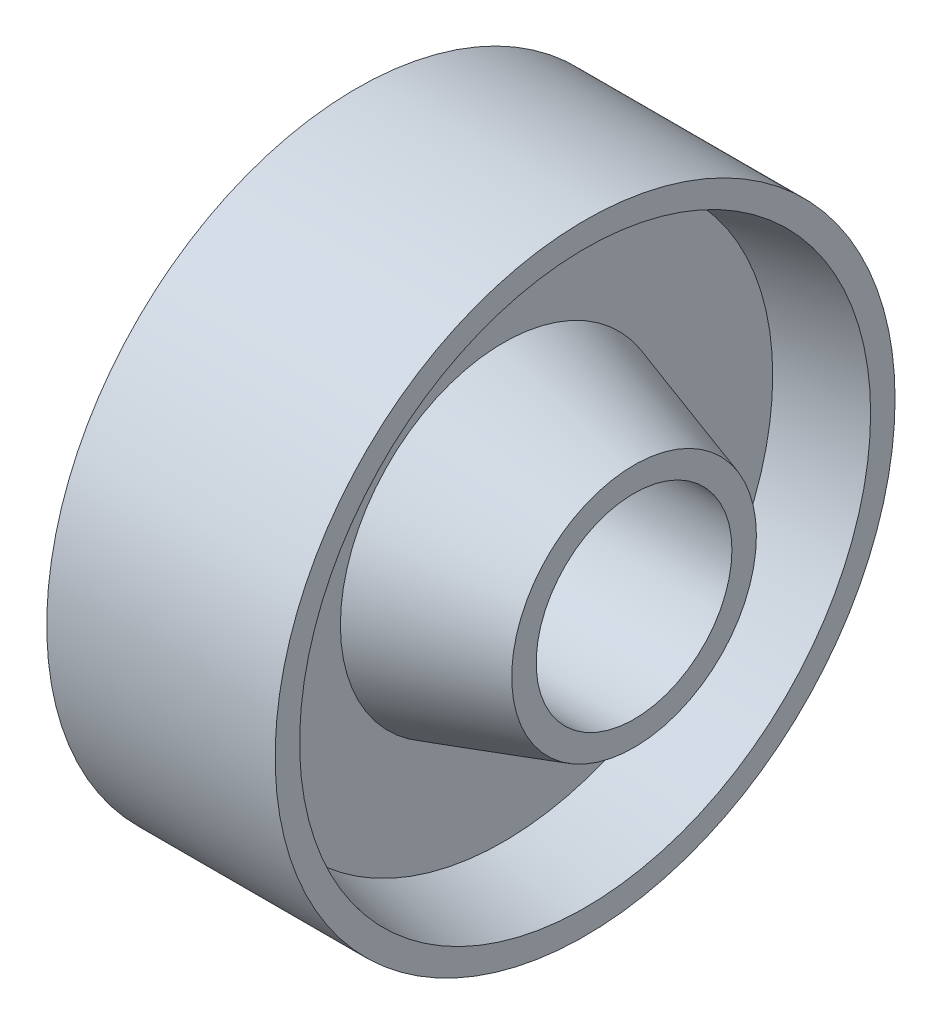
SolidWorks part; units mm, degrees
ref_plane "Front Plane" through (0, 0, 0) normal (0, 0, 1) x (1, 0, 0)
ref_plane "Top Plane" through (0, 0, 0) normal (0, 1, 0) x (1, 0, 0)
ref_plane "Right Plane" through (0, 0, 0) normal (1, 0, 0) x (0, 0, -1)
sketch "Sketch1" plane through (0, 0, 0) normal (0, 0, 1) x (1, 0, 0)
  line L0 (90.0086, 0) -> (0, 0) construction
  line L1 (0, 0) -> (0, 28) construction
  line L2 (20, 12) -> (20, 15)
  line L3 (-20, 12) -> (-20, 15)
  line L4 (20, 15) -> (4, 20)
  line L5 (-20, 15) -> (-4, 20)
  line L6 (4, 20) -> (4, 33)
  line L7 (-4, 20) -> (-4, 33)
  line L8 (4, 33) -> (14, 35)
  line L9 (-4, 33) -> (-14, 35)
  line L10 (14, 35) -> (14, 38)
  line L11 (-14, 35) -> (-14, 38)
  line L12 (-14, 38) -> (14, 38)
  line L13 (-20, 12) -> (20, 12)
  dimension "D1" = 24
  dimension "D2" = 30
  dimension "D3" = 40
  dimension "D4" = 66
  dimension "D5" = 70
  dimension "D6" = 76
  dimension "D7" = 40
  dimension "D8" = 8
  dimension "D9" = 28
revolve "Revolve1" add sketch "Sketch1" angle 360 about L0
